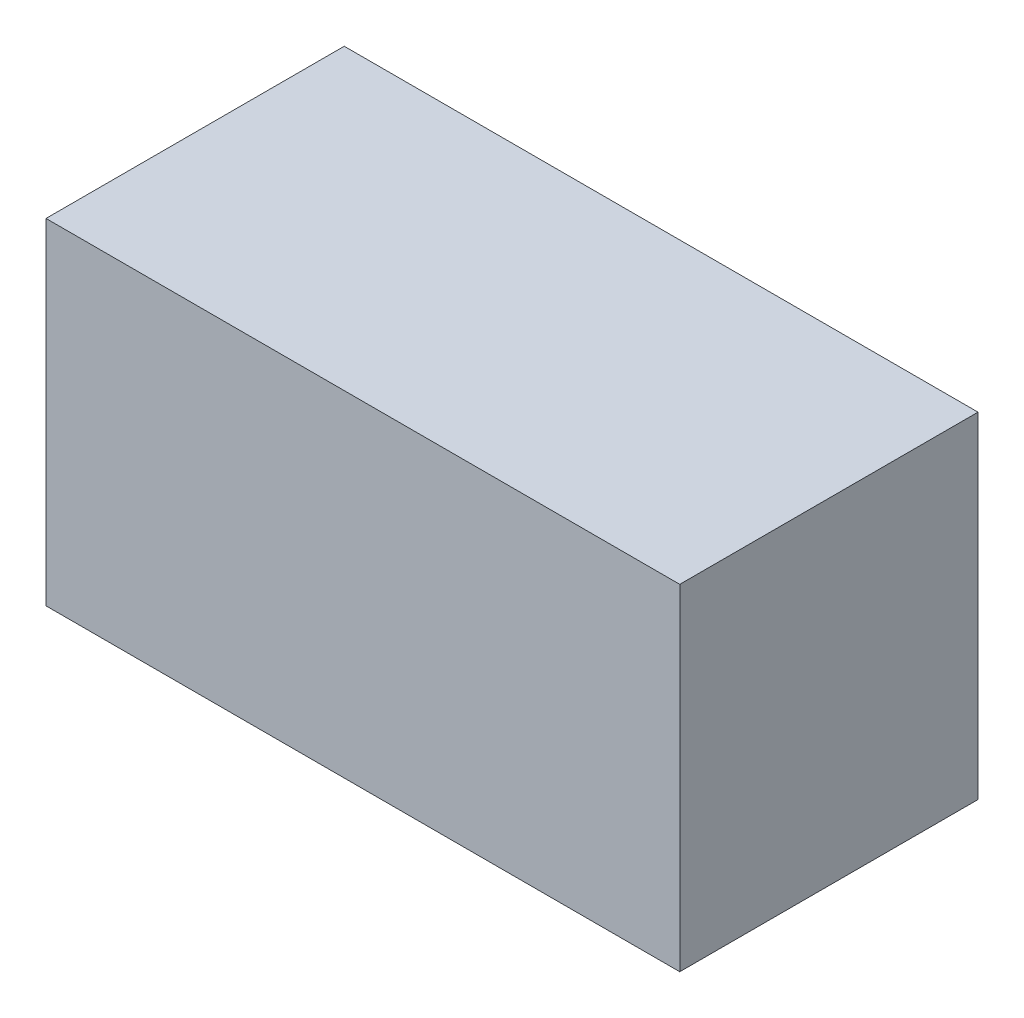
SolidWorks part; units mm, degrees
material "POM Acetalkopolymer"
ref_plane "Ebene vorne" through (0, 0, 0) normal (0, 0, 1) x (1, 0, 0)
ref_plane "Ebene oben" through (0, 0, 0) normal (0, 1, 0) x (1, 0, 0)
ref_plane "Ebene rechts" through (0, 0, 0) normal (1, 0, 0) x (0, 0, -1)
sketch "-body" plane through (0, 0, 0) normal (0, 0, 1) x (1, 0, 0)
  line L1 (-8.5, 4.5) -> (8.5, 4.5)
  line L2 (-8.5, 4.5) -> (-8.5, -4.5)
  line L3 (-8.5, -4.5) -> (8.5, -4.5)
  line L4 (8.5, 4.5) -> (8.5, -4.5)
  line L5 (-8.5, 4.5) -> (8.5, -4.5) construction
  line L6 (-8.5, -4.5) -> (8.5, 4.5) construction
  point P0 (0, 0)
  dimension "D1" = 17
  dimension "D2" = 9
extrude "body" add sketch "-body" along normal mid plane 8
